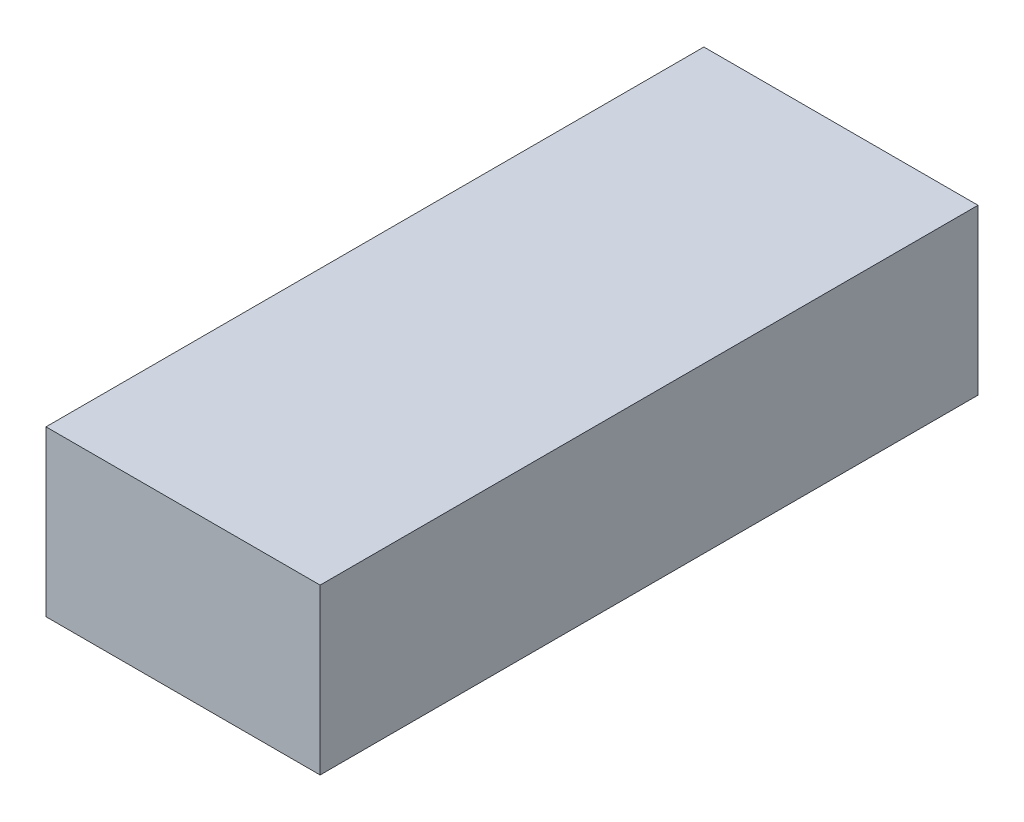
SolidWorks part; units mm, degrees
ref_plane "Front Plane" through (0, 0, 0) normal (0, 0, 1) x (1, 0, 0)
ref_plane "Top Plane" through (0, 0, 0) normal (0, 1, 0) x (1, 0, 0)
ref_plane "Right Plane" through (0, 0, 0) normal (1, 0, 0) x (0, 0, -1)
sketch "Sketch1" plane through (0, 0, 0) normal (0, 1, 0) x (1, 0, 0)
  line L1 (-2.5, 6) -> (2.5, 6)
  line L2 (-2.5, 6) -> (-2.5, -6)
  line L3 (-2.5, -6) -> (2.5, -6)
  line L4 (2.5, 6) -> (2.5, -6)
  line L5 (-2.5, 6) -> (2.5, -6) construction
  line L6 (-2.5, -6) -> (2.5, 6) construction
  point P0 (0, 0)
  dimension "D1" = 5
  dimension "D2" = 12
extrude "Boss-Extrude1" add sketch "Sketch1" along normal blind 3
